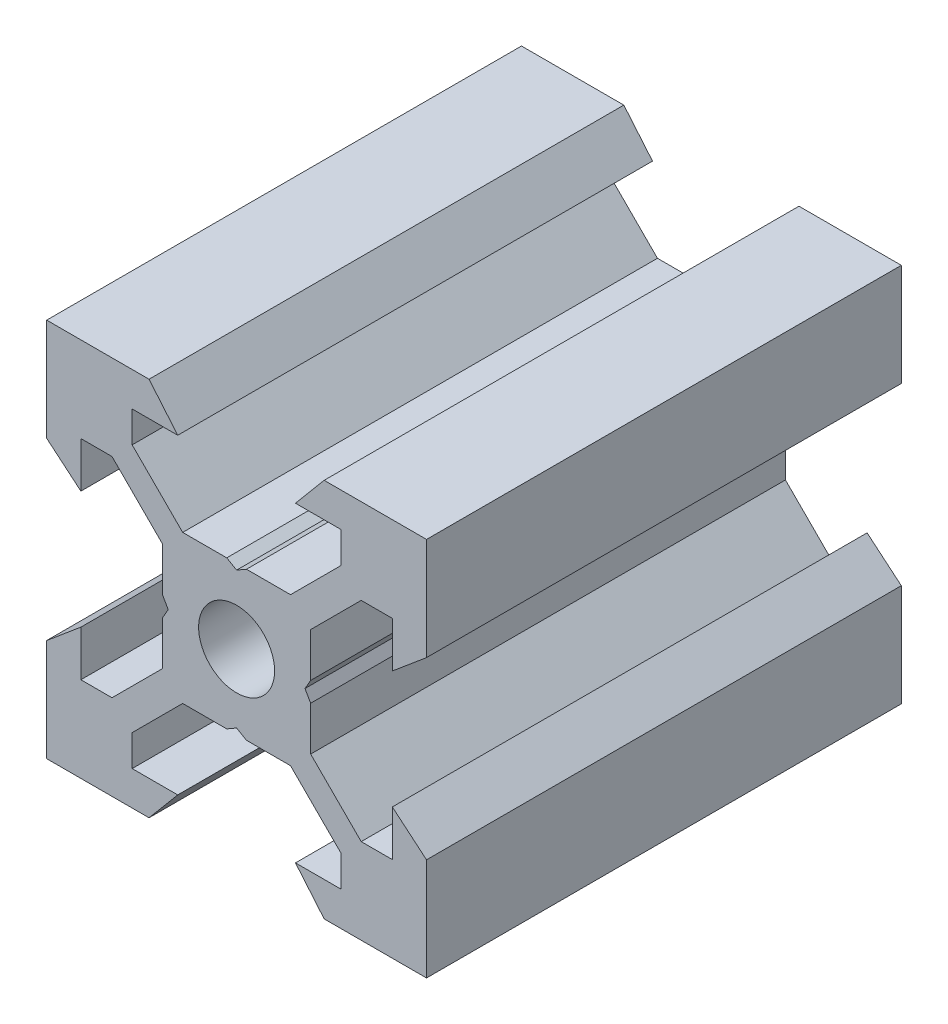
SolidWorks part; units mm, degrees
ref_plane "Front Plane" through (0, 0, 0) normal (0, 0, 1) x (1, 0, 0)
ref_plane "Top Plane" through (0, 0, 0) normal (0, 1, 0) x (1, 0, 0)
ref_plane "Right Plane" through (0, 0, 0) normal (1, 0, 0) x (0, 0, -1)
sketch "Sketch1" plane through (0, 0, 0) normal (0, 0, 1) x (1, 0, 0)
  line L0 (10, 10) -> (4.6104, 10) construction
  line L1 (10, 10) -> (10, 4.6104) construction
  line L2 (10, -10) -> (10, -4.6104) construction
  line L3 (10, -10) -> (4.6104, -10) construction
  line L4 (10, 10) -> (10, 4.6104)
  line L5 (6.5607, 5.5) -> (8.2, 5.5)
  line L6 (5.5, 8.2) -> (5.5, 6.5607)
  line L7 (10, 10) -> (4.6104, 10)
  line L8 (10, 10) -> (10, 4.6104)
  line L9 (6.5607, 5.5) -> (3.9, 2.8393)
  line L10 (5.5, 6.5607) -> (2.8393, 3.9)
  line L11 (10, 4.6104) -> (8.2, 3.1)
  line L12 (4.6104, 10) -> (3.1, 8.2)
  line L13 (8.2, 3.1) -> (8.2, 5.5)
  line L14 (3.1, 8.2) -> (5.5, 8.2)
  line L15 (-6.5607, 5.5) -> (-8.2, 5.5)
  line L16 (6.5607, -5.5) -> (8.2, -5.5)
  line L17 (3.1, -8.2) -> (5.5, -8.2)
  line L18 (8.2, -3.1) -> (8.2, -5.5)
  line L19 (4.6104, -10) -> (3.1, -8.2)
  line L20 (10, -4.6104) -> (8.2, -3.1)
  line L21 (0.5196, -3.9) -> (0, -3.6)
  line L22 (0.5196, 3.9) -> (0, 3.6)
  line L23 (3.6, 0) -> (3.9, -0.5196)
  line L24 (3.9, 0.5196) -> (3.6, 0)
  line L25 (3.9, 0.5196) -> (3.9, 2.8393)
  line L26 (2.8393, 3.9) -> (0.5196, 3.9)
  line L27 (3.9, -2.8393) -> (3.9, -0.5196)
  line L28 (2.8393, -3.9) -> (0.5196, -3.9)
  line L29 (5.5, -6.5607) -> (2.8393, -3.9)
  line L30 (6.5607, -5.5) -> (3.9, -2.8393)
  line L31 (10, -10) -> (10, -4.6104)
  line L32 (10, -10) -> (4.6104, -10)
  line L33 (5.5, -8.2) -> (5.5, -6.5607)
  line L34 (-6.5607, -5.5) -> (-8.2, -5.5)
  line L35 (10, -10) -> (10, -4.6104)
  line L36 (0, 0) -> (0, 8.2) construction
  line L37 (-10, -10) -> (-4.6104, -10) construction
  line L38 (-10, -10) -> (-10, -4.6104) construction
  line L39 (-10, 10) -> (-10, 4.6104) construction
  line L40 (-10, 10) -> (-4.6104, 10) construction
  line L41 (-10, -10) -> (-10, -4.6104)
  line L43 (-5.5, -8.2) -> (-5.5, -6.5607)
  line L44 (-10, -10) -> (-4.6104, -10)
  line L45 (-10, -10) -> (-10, -4.6104)
  line L46 (-6.5607, -5.5) -> (-3.9, -2.8393)
  line L47 (-5.5, -6.5607) -> (-2.8393, -3.9)
  line L48 (-2.8393, -3.9) -> (-0.5196, -3.9)
  line L49 (-3.9, -2.8393) -> (-3.9, -0.5196)
  line L50 (-2.8393, 3.9) -> (-0.5196, 3.9)
  line L51 (-3.9, 0.5196) -> (-3.9, 2.8393)
  line L52 (-3.9, 0.5196) -> (-3.6, 0)
  line L53 (-3.6, 0) -> (-3.9, -0.5196)
  line L54 (-0.5196, 3.9) -> (0, 3.6)
  line L55 (-0.5196, -3.9) -> (0, -3.6)
  line L56 (-10, -4.6104) -> (-8.2, -3.1)
  line L57 (-4.6104, -10) -> (-3.1, -8.2)
  line L58 (-8.2, -3.1) -> (-8.2, -5.5)
  line L59 (-3.1, -8.2) -> (-5.5, -8.2)
  line L60 (-10, -10) -> (10, -10) construction
  line L61 (-10, -10) -> (-10, 10) construction
  line L62 (-3.1, 8.2) -> (-5.5, 8.2)
  line L63 (-8.2, 3.1) -> (-8.2, 5.5)
  line L64 (-4.6104, 10) -> (-3.1, 8.2)
  line L65 (-10, 4.6104) -> (-8.2, 3.1)
  line L66 (-5.5, 6.5607) -> (-2.8393, 3.9)
  line L67 (-6.5607, 5.5) -> (-3.9, 2.8393)
  line L68 (-10, 10) -> (-10, 4.6104)
  line L69 (-10, 10) -> (-4.6104, 10)
  line L70 (-5.5, 8.2) -> (-5.5, 6.5607)
  line L71 (-10, 10) -> (10, 10) construction
  line L72 (-10, 10) -> (-10, 4.6104)
  line L73 (10, -10) -> (10, 10) construction
  line L74 (-10, -10) -> (10, 10) construction
  line L75 (-10, 10) -> (10, -10) construction
  circle A0 centre (0, 0) radius 2
  dimension "D7" = 4
  dimension "D1" = 20
  dimension "D2" = 5.3896
  dimension "D3" = 4.5
  dimension "D4" = 50
  dimension "D5" = 1.8
  dimension "D6" = 1.5104
  dimension "D8" = 5.5
  dimension "D9" = 120
  dimension "D10" = 0.3
  dimension "D11" = 2.3197
  dimension "D12" = 7.8
  dimension "D13" = 7.8
  dimension "D14" = 1.5
  dimension "D15" = 2.6607
extrude "Boss-Extrude1" add sketch "Sketch1" along normal mid plane 25 contours L70 L62 L64 L69 L68 L65 L63 L15 L67 L51 L52 L53 L49 L46 L34 L58 L56 L41 L44 L57 L59 L43 L47 L48 L55 L21 L28 L29 L33 L17 L19 L32 L31 L20 L18 L16 L30 L27 L23 L24 L25 L9 L5 L13 L11 L4 L7 L12 L14 L6 L10
